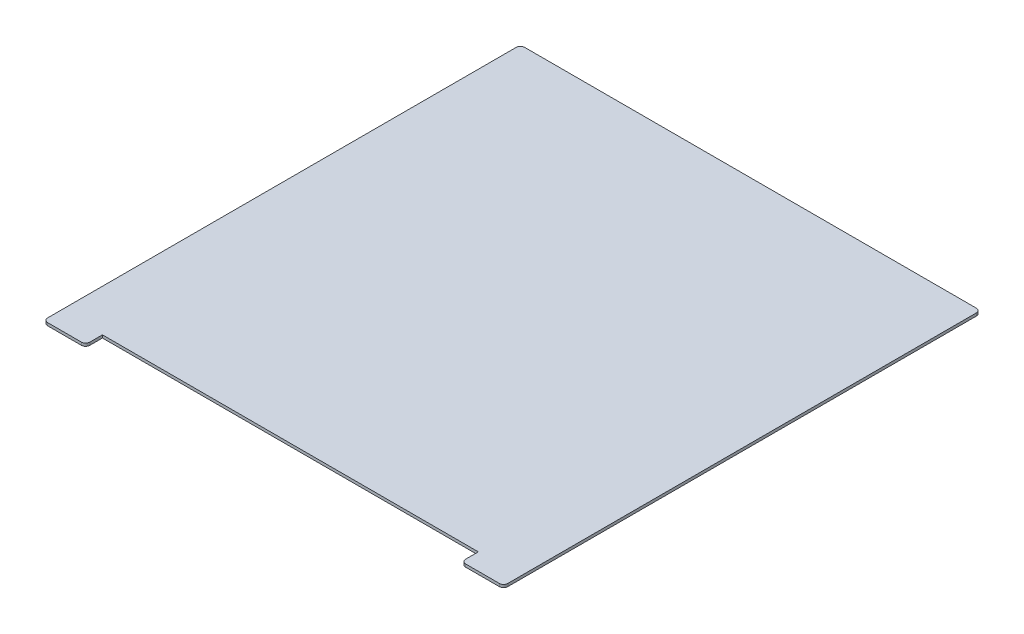
SolidWorks part; units mm, degrees
ref_plane "Front Plane" through (0, 0, 0) normal (0, 0, 1) x (1, 0, 0)
ref_plane "Top Plane" through (0, 0, 0) normal (0, 1, 0) x (1, 0, 0)
ref_plane "Right Plane" through (0, 0, 0) normal (1, 0, 0) x (0, 0, -1)
sketch "Sketch1" plane through (0, 0, 0) normal (0, 1, 0) x (1, 0, 0)
  line L0 (-268, -197.6497) -> (-268, -185.6497)
  line L1 (-298, 142.3503) -> (30, 142.3503)
  line L2 (-298, 142.3503) -> (-298, -197.6497)
  line L3 (-298, -197.6497) -> (-268, -197.6497)
  line L4 (30, 142.3503) -> (30, -197.6497)
  line L5 (-268, -185.6497) -> (0, -185.6497)
  line L6 (0, -185.6497) -> (0, -197.6497)
  line L7 (0, -197.6497) -> (30, -197.6497)
  dimension "D1" = 328
  dimension "D2" = 340
  dimension "D3" = 328
  dimension "D4" = 30
  dimension "D5" = 30
extrude "Boss-Extrude1" add sketch "Sketch1" along normal blind 2
fillet "Fillet1" radius 3 6 edges at (30, 1, -142.3503) (-298, 1, -142.3503) (-268, 1, 197.6497) (-298, 1, 197.6497) (30, 1, 197.6497) (0, 1, 197.6497)
